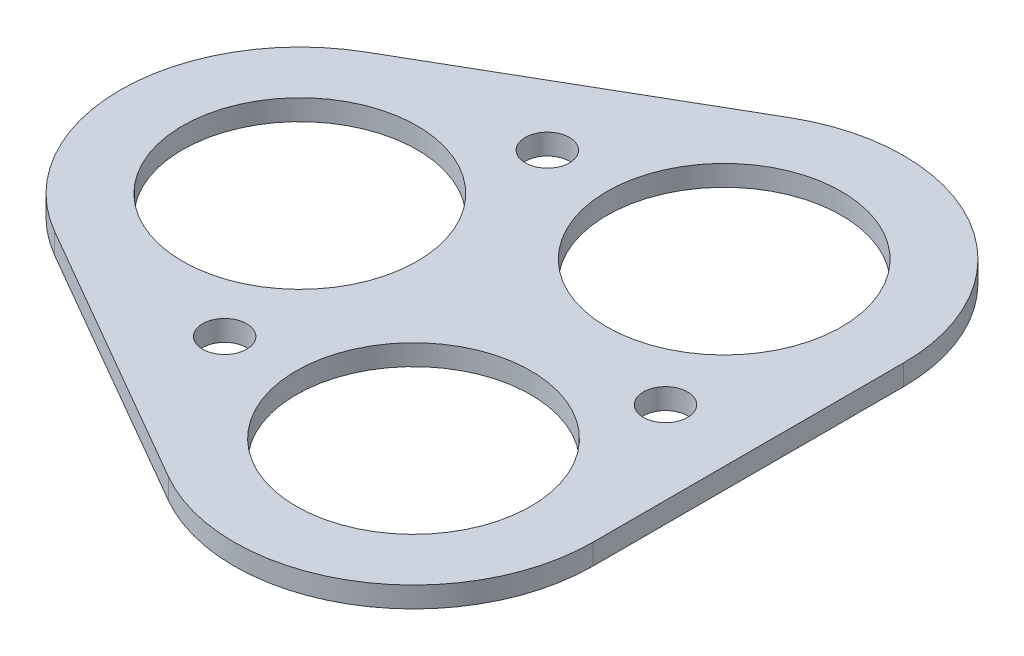
SolidWorks part; units mm, degrees
ref_plane "Front Plane" through (0, 0, 0) normal (0, 0, 1) x (1, 0, 0)
ref_plane "Top Plane" through (0, 0, 0) normal (0, 1, 0) x (1, 0, 0)
ref_plane "Right Plane" through (0, 0, 0) normal (1, 0, 0) x (0, 0, -1)
sketch "Sketch1" plane through (0, 0, 0) normal (0, 1, 0) x (1, 0, 0)
  line L0 (-15.8043, -11.2583) -> (3.6812, -22.5083)
  line L1 (23.1812, -11.25) -> (23.1812, 11.25)
  line L2 (3.6812, 22.5083) -> (-15.8043, 11.2583)
  line L3 (10.1812, -11.25) -> (3.6861, 0) construction
  line L4 (-9.3043, 0) -> (3.6861, 0) construction
  line L5 (10.1812, 11.25) -> (3.6861, 0) construction
  arc A0 (-15.8043, 11.2583) -> (-15.8043, -11.2583) centre (-9.3043, 0) ccw
  arc A1 (3.6812, -22.5083) -> (23.1812, -11.25) centre (10.1812, -11.25) ccw
  arc A2 (23.1812, 11.25) -> (3.6812, 22.5083) centre (10.1812, 11.25) ccw
  circle A3 centre (-9.3043, 0) radius 8.5
  circle A4 centre (-3.0615, 11.6872) radius 1.6
  circle A5 centre (17.1812, 0) radius 1.6
  circle A6 centre (10.1812, -11.25) radius 8.5
  circle A7 centre (10.1812, 11.25) radius 8.5
  circle A8 centre (-3.0615, -11.6872) radius 1.6
  point P21 (3.6861, 0)
  dimension "D1" = 3.2
  dimension "D2" = 17
  dimension "D5" = 13
  dimension "D3" = 19.4856
  dimension "D4" = 22.5
extrude "Boss-Extrude1" add sketch "Sketch1" along normal blind 1.5
